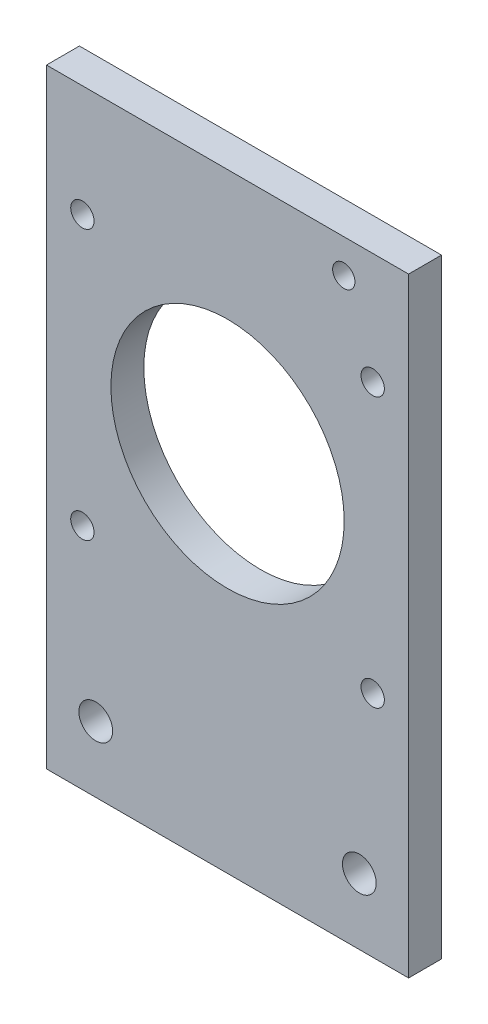
SolidWorks part; units mm, degrees
ref_plane "Front Plane" through (0, 0, 0) normal (0, 0, 1) x (1, 0, 0)
ref_plane "Top Plane" through (0, 0, 0) normal (0, 1, 0) x (1, 0, 0)
ref_plane "Right Plane" through (0, 0, 0) normal (1, 0, 0) x (0, 0, -1)
sketch "Sketch2" plane through (0, 0, 0) normal (0, 0, 1) x (1, 0, 0)
  line L0 (-55, 60.6) -> (55, 60.6) construction
  line L1 (-34.925, 0) -> (34.925, 0)
  line L2 (-34.925, 0) -> (-34.925, 70.1)
  line L3 (-34.925, 70.1) -> (34.925, 70.1) construction
  line L4 (34.925, 0) -> (34.925, 70.1)
  line L5 (0, 60.6) -> (0, 0) construction
  line L6 (0, 60.6) -> (0, 70.1) construction
  line L7 (-34.925, 25.4) -> (34.925, 25.4) construction
  line L10 (34.925, 102.6) -> (-34.925, 102.6) construction
  line L11 (34.925, 70.1) -> (34.925, 102.6)
  line L12 (34.925, 102.6) -> (-34.925, 102.6) construction
  line L13 (-34.925, 102.6) -> (-34.925, 70.1)
  line L14 (34.925, 102.6) -> (34.925, 117.6)
  line L15 (34.925, 117.6) -> (-34.925, 117.6)
  line L16 (-34.925, 102.6) -> (-34.925, 117.6)
  line L17 (-34.925, 25.4) -> (34.925, 25.4) construction
  circle A0 centre (-55, 60.6) radius 3 construction
  circle A1 centre (55, 60.6) radius 3 construction
  circle A2 centre (-55, 60.6) radius 15 construction
  circle A3 centre (55, 60.6) radius 15 construction
  circle A6 centre (0, 70.1) radius 22.5
  circle A7 centre (-55, 60.6) radius 15.6 construction
  point P6 (0, 0)
  dimension "D1" = 6
  dimension "D2" = 30
  dimension "D5" = 45
  dimension "D9" = 15
  dimension "D3" = 110
  dimension "D4" = 9.5
  dimension "D6" = 69.85
  dimension "D7" = 0.6
  dimension "D8" = 32.5
  dimension "D10" = 25.4
  dimension "D12" = 44.7
extrude "Boss-Extrude1" add sketch "Sketch2" along normal mid plane 6.35
sketch "Sketch3" plane through (0, 0, 3.175) normal (0, 0, 1) x (1, 0, 0)
  line L0 (34.925, 117.6) -> (-34.925, 117.6) construction
  line L1 (-34.925, 0) -> (-25.425, 0) construction
  line L2 (-34.925, 0) -> (-34.925, 12.7) construction
  line L3 (-34.925, 12.7) -> (-25.425, 12.7) construction
  line L4 (-25.425, 0) -> (-25.425, 12.7) construction
  line L5 (34.925, 0) -> (25.425, 0) construction
  line L6 (34.925, 0) -> (34.925, 12.7) construction
  line L7 (34.925, 12.7) -> (25.425, 12.7) construction
  line L8 (25.425, 0) -> (25.425, 12.7) construction
  line L9 (34.925, 0) -> (34.925, 117.6) construction
  circle A0 centre (-25.425, 12.7) radius 3.2576
  circle A1 centre (25.425, 12.7) radius 3.2576
  circle A4 centre (22.425, 111.1) radius 2.15
  dimension "D1" = 12.7
  dimension "D2" = 6.5151
  dimension "D4" = 12.5
  dimension "D7" = 4.3
  dimension "D3" = 9.5
  dimension "D9" = 6.5
extrude "Cut-Extrude1" cut sketch "Sketch3" against normal through all both and the other way through all
sketch "Sketch4" plane through (0, 0, 3.175) normal (0, 0, 1) x (1, 0, 0)
  circle A0 centre (28, 96.1) radius 2.25 construction
  circle A1 centre (-28, 44.1) radius 2.25 construction
  circle A2 centre (28, 44.1) radius 2.25 construction
  circle A3 centre (28, 96.1) radius 2.25
  circle A4 centre (-28, 44.1) radius 2.25
  circle A5 centre (28, 44.1) radius 2.25
  circle A6 centre (-28, 96.1) radius 2.25
extrude "Cut-Extrude2" cut sketch "Sketch4" against normal blind 10
